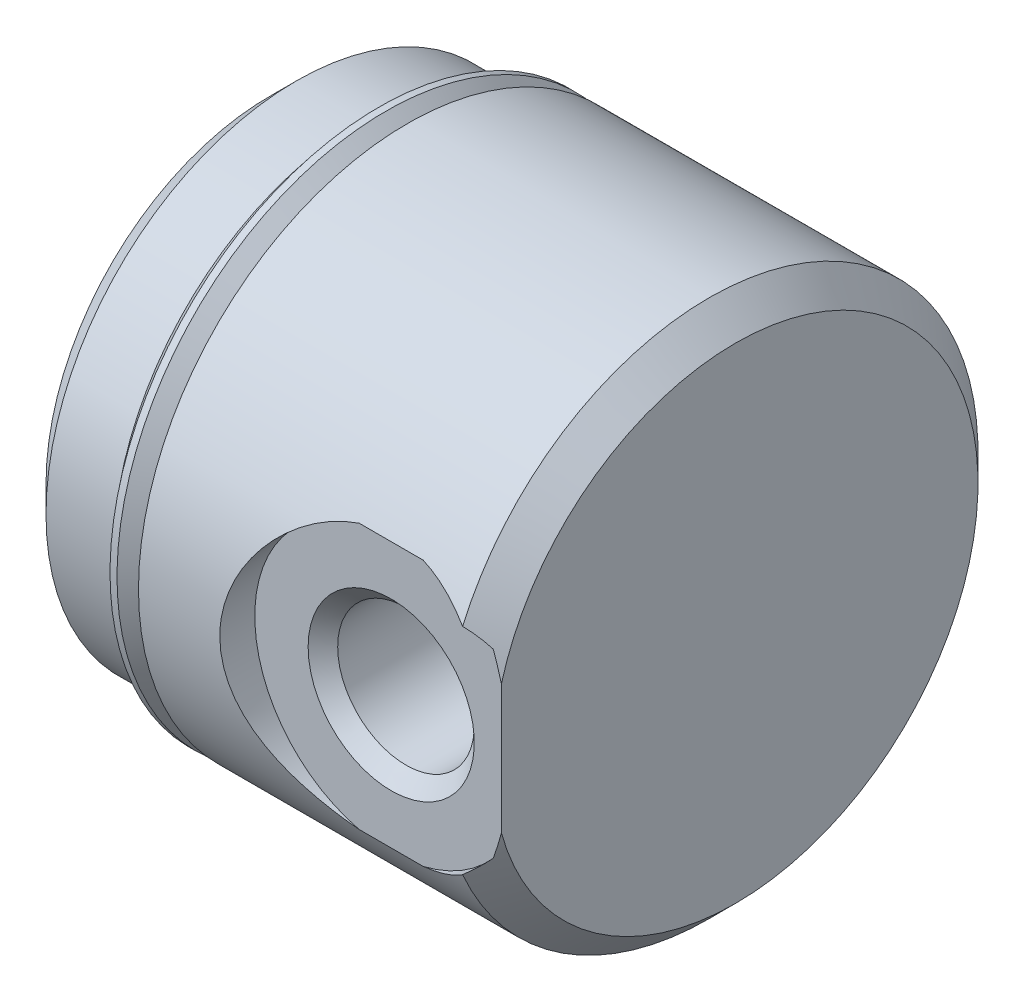
SolidWorks part; units mm, degrees
ref_plane "Front Plane" through (0, 0, 0) normal (0, 0, 1) x (1, 0, 0)
ref_plane "Top Plane" through (0, 0, 0) normal (0, 1, 0) x (1, 0, 0)
ref_plane "Right Plane" through (0, 0, 0) normal (1, 0, 0) x (0, 0, -1)
ref_plane "Plane1" through (0, 0, 0) normal (0, 0, 1) x (1, 0, 0)
sketch "Sketch1" plane through (0, 0, 0) normal (0, 0, 1) x (1, 0, 0)
  line L0 (0, 0) -> (0, 6.5088)
  line L1 (0, 6.5088) -> (0.762, 7.2708)
  line L2 (0.762, 7.2708) -> (2.7178, 7.2708)
  line L3 (2.7178, 7.2708) -> (3.3528, 6.6357)
  line L4 (3.3528, 6.6357) -> (3.9878, 6.6357)
  line L5 (3.9878, 6.6357) -> (3.9878, 7.8105)
  line L6 (3.9878, 7.8105) -> (12.7508, 7.8105)
  line L7 (12.7508, 7.8105) -> (13.5128, 7.0485)
  line L8 (13.5128, 7.0485) -> (13.5128, 0)
  line L9 (13.5128, 0) -> (0, 0)
  line L10 (13.5128, 0) -> (0, 0) construction
revolve "Revolve1" add sketch "Sketch1" angle 360 about L10
ref_plane "Plane2" through (0, 0, 0) normal (0, 0, 1) x (1, 0, 0)
sketch "Sketch2" plane through (0, 0, 0) normal (0, 0, 1) x (1, 0, 0)
  line L0 (0, 0) -> (0, 1.9558)
  line L1 (0, 1.9558) -> (12.2936, 1.9558)
  line L2 (12.2936, 1.9558) -> (13.4228, 0)
  line L3 (13.4228, 0) -> (0, 0)
  line L4 (13.4228, 0) -> (0, 0) construction
revolve "Cut-Revolve1" cut sketch "Sketch2" angle 360 about L4
ref_plane "Plane3" through (0, 0, 0) normal (0, 1, 0) x (1, 0, 0)
sketch "Sketch3" plane through (0, 0, 0) normal (0, 1, 0) x (1, 0, 0)
  line L0 (10.3124, 0) -> (12.2961, 0)
  line L1 (12.2961, 0) -> (12.2961, -6.3652)
  line L2 (12.2961, -6.3652) -> (12.7254, -6.7945)
  line L3 (12.7254, -6.7945) -> (14.2748, -6.7945)
  line L4 (14.2748, -6.7945) -> (14.2748, -7.8105)
  line L5 (14.2748, -7.8105) -> (10.3124, -7.8105)
  line L6 (10.3124, -7.8105) -> (10.3124, 0)
  line L7 (10.3124, -7.8105) -> (10.3124, 0) construction
revolve "Cut-Revolve2" cut sketch "Sketch3" angle 360 about L7
ref_plane "Plane4" through (0, 0, 0) normal (0, 0, 1) x (1, 0, 0)
sketch "Sketch4" plane through (0, 0, 0) normal (0, 0, 1) x (1, 0, 0)
  line L0 (3.1602, 7.8105) -> (3.1602, 7.7263)
  line L1 (3.1602, 7.7263) -> (3.8708, 7.0158)
  line L2 (3.8708, 6.8362) -> (3.6703, 6.6357)
  line L3 (3.6703, 6.6357) -> (3.3528, 6.6357)
  line L4 (3.3528, 6.6357) -> (3.3528, 6.3818)
  line L5 (3.3528, 6.3818) -> (3.9878, 6.3818)
  line L6 (3.9878, 6.3818) -> (3.9878, 7.1861)
  line L7 (3.9878, 7.1861) -> (3.3634, 7.8105)
  line L8 (3.3634, 7.8105) -> (3.1602, 7.8105)
  line L9 (3.9878, 0) -> (3.3528, 0) construction
  arc A0 (3.8708, 7.0158) -> (3.8708, 6.8362) centre (3.781, 6.926) cw
revolve "Revolve2" add sketch "Sketch4" angle 360 about L9
